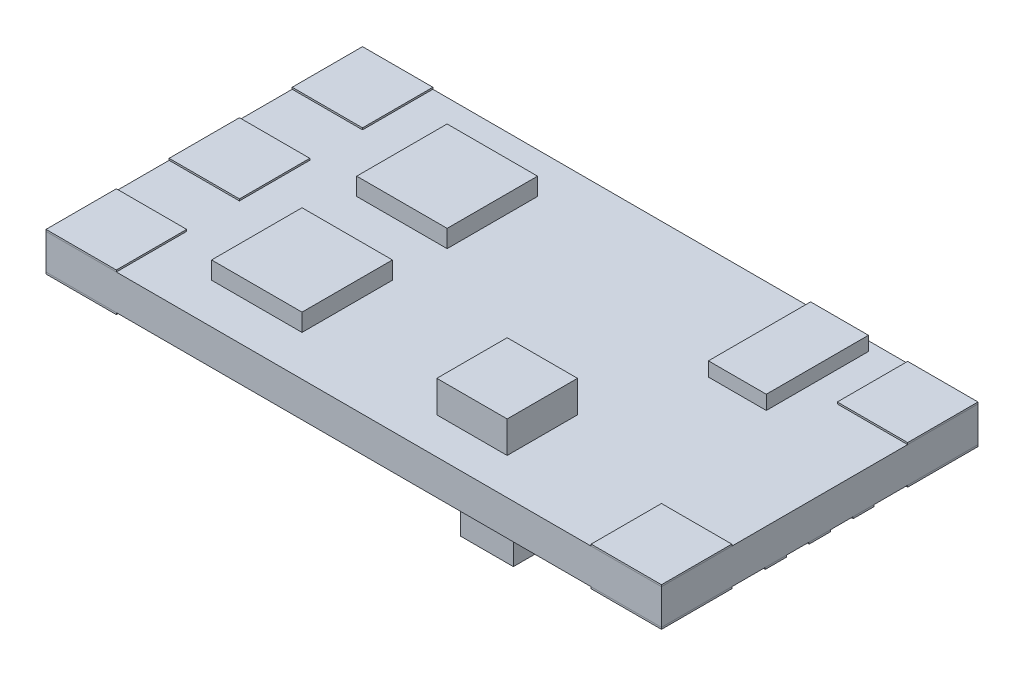
SolidWorks part; units mm, degrees
ref_plane "Front Plane" through (0, 0, 0) normal (0, 0, 1) x (1, 0, 0)
ref_plane "Top Plane" through (0, 0, 0) normal (0, 1, 0) x (1, 0, 0)
ref_plane "Right Plane" through (0, 0, 0) normal (1, 0, 0) x (0, 0, -1)
sketch "Sketch1" plane through (0, 0, 0) normal (0, 1, 0) x (1, 0, 0)
  line L1 (-17.5, -9) -> (17.5, -9)
  line L2 (-17.5, -9) -> (-17.5, 9)
  line L3 (-17.5, 9) -> (17.5, 9)
  line L4 (17.5, -9) -> (17.5, 9)
  line L5 (0, 9) -> (0, -9) construction
  line L6 (-17.5, 0) -> (17.5, 0) construction
  point P0 (0, 0)
  dimension "D1" = 35
  dimension "D2" = 18
extrude "Boss-Extrude1" add sketch "Sketch1" along normal blind 2
sketch "Sketch2" plane through (0, 2, 0) normal (0, 1, 0) x (1, 0, 0)
  line L1 (8.5094, 2.6608) -> (11.8, 2.6608)
  line L2 (8.5094, 2.6608) -> (8.5094, 8.4708)
  line L3 (8.5094, 8.4708) -> (11.8, 8.4708)
  line L4 (11.8, 2.6608) -> (11.8, 8.4708)
  line L5 (10.1547, 8.4708) -> (10.1547, 2.6608) construction
  line L6 (8.5094, 5.5658) -> (11.8, 5.5658) construction
  point P0 (10.1547, 5.5658)
extrude "Boss-Extrude2" add sketch "Sketch2" along normal blind 0.8 separate body
sketch "Sketch3" plane through (0, 2, 0) normal (0, 1, 0) x (1, 0, 0)
  line L1 (2.6479, -6.9231) -> (6.6479, -6.9231)
  line L2 (2.6479, -6.9231) -> (2.6479, -2.9231)
  line L3 (2.6479, -2.9231) -> (6.6479, -2.9231)
  line L4 (6.6479, -6.9231) -> (6.6479, -2.9231)
  line L5 (4.6479, -2.9231) -> (4.6479, -6.9231) construction
  line L6 (2.6479, -4.9231) -> (6.6479, -4.9231) construction
  point P0 (4.6479, -4.9231)
  dimension "D1" = 4
extrude "Boss-Extrude3" add sketch "Sketch3" along normal blind 1.8 separate body
sketch "Sketch4" plane through (0, 2, 0) normal (0, 1, 0) x (1, 0, 0)
  line L0 (-17.5, 0) -> (17.5, 0) construction
  line L5 (-17.5, 9) -> (-17.5, -9) construction
  line L6 (17.5, -9) -> (17.5, 9) construction
  line L7 (-10.3861, -6.697) -> (-5.2444, -6.697)
  line L8 (-10.3861, -6.697) -> (-10.3861, -1.5553)
  line L9 (-10.3861, -1.5553) -> (-5.2444, -1.5553)
  line L10 (-5.2444, -6.697) -> (-5.2444, -1.5553)
  line L11 (-7.8153, -1.5553) -> (-7.8153, -6.697) construction
  line L12 (-10.3861, -4.1261) -> (-5.2444, -4.1261) construction
  line L13 (-10.3861, 1.5553) -> (-5.2444, 1.5553)
  line L14 (-5.2444, 6.697) -> (-5.2444, 1.5553)
  line L15 (-10.3861, 6.697) -> (-5.2444, 6.697)
  line L16 (-10.3861, 6.697) -> (-10.3861, 1.5553)
  point P4 (-7.8153, -4.1261)
extrude "Boss-Extrude4" add sketch "Sketch4" along normal blind 1 separate body
sketch "Sketch5" plane through (0, 2, 0) normal (0, 1, 0) x (1, 0, 0)
  line L0 (-17.5, 9) -> (-17.5, -9) construction
  line L1 (-13.5, 5) -> (-17.5, 5)
  line L2 (-13.5, 5) -> (-13.5, 9)
  line L3 (-13.5, 9) -> (-17.5, 9)
  line L4 (-17.5, 5) -> (-17.5, 9)
  line L5 (-15.5, 9) -> (-15.5, 5) construction
  line L6 (-13.5, 7) -> (-17.5, 7) construction
  line L7 (-13.5, -2) -> (-17.5, -2)
  line L8 (-13.5, -2) -> (-13.5, 2)
  line L9 (-13.5, 2) -> (-17.5, 2)
  line L10 (-17.5, -2) -> (-17.5, 2)
  line L11 (-15.5, 2) -> (-15.5, -2) construction
  line L12 (-13.5, 0) -> (-17.5, 0) construction
  line L13 (13.5, -9) -> (17.5, -9)
  line L14 (-13.5, -5) -> (-17.5, -5)
  line L15 (-13.5, -5) -> (-13.5, -9)
  line L16 (-13.5, -9) -> (-17.5, -9)
  line L17 (-17.5, -5) -> (-17.5, -9)
  line L18 (-15.5, -9) -> (-15.5, -5) construction
  line L19 (-13.5, -7) -> (-17.5, -7) construction
  line L20 (13.5, 5) -> (17.5, 5)
  line L21 (13.5, 5) -> (13.5, 9)
  line L22 (13.5, 9) -> (17.5, 9)
  line L23 (17.5, 5) -> (17.5, 9)
  line L24 (15.5, 9) -> (15.5, 5) construction
  line L25 (13.5, 7) -> (17.5, 7) construction
  line L26 (17.5, -5) -> (17.5, -9)
  line L27 (13.5, -5) -> (17.5, -5)
  line L28 (13.5, -5) -> (13.5, -9)
  point P0 (-15.5, 7)
  point P4 (-15.5, 0)
  point P10 (-15.5, -7)
  point P14 (15.5, 7)
  dimension "D1" = 4
extrude "Boss-Extrude5" add sketch "Sketch5" along normal blind 0.1 separate body
ref_plane "Plane1" through (0, 1, 0) normal (0, 1, 0) x (1, 0, 0)
mirror "Mirror1" about plane through (0, 1, 0) normal (0, 1, 0) of bodies 106 107 108 109 110
sketch "Sketch6" plane through (0, 0, 0) normal (0, -1, 0) x (1, 0, 0)
  line L0 (-4, 9) -> (-4, -9) construction
  line L1 (-17.5, 9) -> (17.5, 9) construction
  line L2 (17.5, -9) -> (-17.5, -9) construction
  line L3 (-17.5, -9) -> (-17.5, 9) construction
  line L4 (-11.5, -8.238) -> (-4.8052, -8.238)
  line L5 (-11.5, 3.762) -> (-4.8052, 3.762)
  line L6 (-11.5, 3.762) -> (-11.5, 8.238)
  line L7 (-11.5, 8.238) -> (-4.8052, 8.238)
  line L8 (-4.8052, 3.762) -> (-4.8052, 8.238)
  line L9 (-8.1526, 8.238) -> (-8.1526, 3.762) construction
  line L10 (-11.5, 6) -> (-4.8052, 6) construction
  line L11 (-11.5, -2.238) -> (-4.8052, -2.238)
  line L12 (-11.5, -2.238) -> (-11.5, 2.238)
  line L13 (-11.5, 2.238) -> (-4.8052, 2.238)
  line L14 (-4.8052, -2.238) -> (-4.8052, 2.238)
  line L15 (-8.1526, 2.238) -> (-8.1526, -2.238) construction
  line L16 (-11.5, 0) -> (-4.8052, 0) construction
  line L17 (-4.8052, -3.762) -> (-4.8052, -8.238)
  line L18 (-11.5, -3.762) -> (-4.8052, -3.762)
  line L19 (-11.5, -3.762) -> (-11.5, -8.238)
  line L20 (3.5, -3.762) -> (3.5, -8.238)
  line L21 (3.5, -3.762) -> (-3.1948, -3.762)
  line L22 (-3.1948, -3.762) -> (-3.1948, -8.238)
  line L23 (3.5, -8.238) -> (-3.1948, -8.238)
  line L24 (3.5, 2.238) -> (-3.1948, 2.238)
  line L25 (-3.1948, -2.238) -> (-3.1948, 2.238)
  line L26 (3.5, -2.238) -> (-3.1948, -2.238)
  line L27 (3.5, -2.238) -> (3.5, 2.238)
  line L28 (3.5, 8.238) -> (-3.1948, 8.238)
  line L29 (-3.1948, 3.762) -> (-3.1948, 8.238)
  line L30 (3.5, 3.762) -> (-3.1948, 3.762)
  line L31 (3.5, 3.762) -> (3.5, 8.238)
  point P8 (-8.1526, 6)
  point P12 (-8.1526, 0)
  dimension "D1" = 13.5
  dimension "D2" = 6
  dimension "D3" = 6
extrude "Boss-Extrude6" add sketch "Sketch6" along normal blind 0.7 separate body
sketch "Sketch7" plane through (0, 0, 0) normal (0, -1, 0) x (1, 0, 0)
  line L0 (7, 9) -> (7, -9) construction
  line L1 (-17.5, 9) -> (17.5, 9) construction
  line L2 (17.5, -9) -> (-17.5, -9) construction
  line L3 (17.5, 9) -> (17.5, -9) construction
  line L4 (5.5, 4.6444) -> (5.5, 6.2444)
  line L5 (5.5, 6.8222) -> (8.5, 6.8222)
  line L6 (5.5, 6.8222) -> (5.5, 8.4222)
  line L7 (5.5, 8.4222) -> (8.5, 8.4222)
  line L8 (8.5, 6.8222) -> (8.5, 8.4222)
  line L9 (7, 8.4222) -> (7, 6.8222) construction
  line L10 (5.5, 7.6222) -> (8.5, 7.6222) construction
  line L11 (5.5, 4.6444) -> (8.5, 4.6444)
  line L12 (8.5, 4.6444) -> (8.5, 6.2444)
  line L13 (5.5, 6.2444) -> (8.5, 6.2444)
  line L14 (5.5, 2.4667) -> (5.5, 4.0667)
  line L15 (5.5, 2.4667) -> (8.5, 2.4667)
  line L16 (8.5, 2.4667) -> (8.5, 4.0667)
  line L17 (5.5, 4.0667) -> (8.5, 4.0667)
  line L18 (5.5, 0.2889) -> (5.5, 1.8889)
  line L19 (5.5, 0.2889) -> (8.5, 0.2889)
  line L20 (8.5, 0.2889) -> (8.5, 1.8889)
  line L21 (5.5, 1.8889) -> (8.5, 1.8889)
  line L22 (5.5, -1.8889) -> (5.5, -0.2889)
  line L23 (5.5, -1.8889) -> (8.5, -1.8889)
  line L24 (8.5, -1.8889) -> (8.5, -0.2889)
  line L25 (5.5, -0.2889) -> (8.5, -0.2889)
  line L26 (5.5, -4.0667) -> (5.5, -2.4667)
  line L27 (5.5, -4.0667) -> (8.5, -4.0667)
  line L28 (8.5, -4.0667) -> (8.5, -2.4667)
  line L29 (5.5, -2.4667) -> (8.5, -2.4667)
  line L30 (5.5, -6.2444) -> (5.5, -4.6444)
  line L31 (5.5, -6.2444) -> (8.5, -6.2444)
  line L32 (8.5, -6.2444) -> (8.5, -4.6444)
  line L33 (5.5, -4.6444) -> (8.5, -4.6444)
  line L34 (5.5, -8.4222) -> (5.5, -6.8222)
  line L35 (5.5, -8.4222) -> (8.5, -8.4222)
  line L36 (8.5, -8.4222) -> (8.5, -6.8222)
  line L37 (5.5, -6.8222) -> (8.5, -6.8222)
  line L38 (8.5, -8.4222) -> (8.5, -9) construction
  line L39 (8.5, 8.4222) -> (8.5, 9) construction
  line L40 (8.5, 6.8222) -> (8.5, 6.2444) construction
  point P8 (7, 7.6222)
  dimension "D1" = 10.5
  dimension "D3" = 1.6
  dimension "D4" = 3
  dimension "D2" = 8
extrude "Boss-Extrude7" add sketch "Sketch7" along normal blind 1.8 separate body
sketch "Sketch8" plane through (0, 0, 0) normal (0, -1, 0) x (1, 0, 0)
  line L0 (17.5, 9) -> (17.5, -9) construction
  line L1 (15.5, -0.6) -> (17.5, -0.6)
  line L2 (15.5, -0.6) -> (15.5, 0.6)
  line L3 (15.5, 0.6) -> (17.5, 0.6)
  line L4 (17.5, -0.6) -> (17.5, 0.6)
  line L5 (16.5, 0.6) -> (16.5, -0.6) construction
  line L6 (15.5, 0) -> (17.5, 0) construction
  line L7 (15.5, 1.9) -> (17.5, 1.9)
  line L8 (15.5, 1.9) -> (15.5, 3.1)
  line L9 (15.5, 3.1) -> (17.5, 3.1)
  line L10 (17.5, 1.9) -> (17.5, 3.1)
  line L11 (16.5, 3.1) -> (16.5, 1.9) construction
  line L12 (15.5, 2.5) -> (17.5, 2.5) construction
  line L13 (15.5, -3.1) -> (17.5, -3.1)
  line L14 (17.5, -1.9) -> (17.5, -3.1)
  line L15 (15.5, -1.9) -> (17.5, -1.9)
  line L16 (15.5, -1.9) -> (15.5, -3.1)
  point P0 (16.5, 0)
  point P4 (16.5, 2.5)
  point P8 (0, 0)
  point P9 (0, 0)
  dimension "D1" = 2.5
  dimension "D2" = 2
  dimension "D3" = 1.2
extrude "Boss-Extrude8" add sketch "Sketch8" along normal up to surface (0.1 mm away) separate body up to face at (15.5, -0.1, 7)
sketch "Sketch9" plane through (0, 0, 0) normal (0, -1, 0) x (1, 0, 0)
  line L0 (17.5, 9) -> (17.5, -9) construction
  line L1 (11.5, -1) -> (13.5, -1)
  line L2 (11.5, -1) -> (11.5, 1)
  line L3 (11.5, 1) -> (13.5, 1)
  line L4 (13.5, -1) -> (13.5, 1)
  line L5 (12.5, 1) -> (12.5, -1) construction
  line L6 (11.5, 0) -> (13.5, 0) construction
  point P0 (12.5, 0)
  dimension "D1" = 5
  dimension "D2" = 2
extrude "Boss-Extrude9" add sketch "Sketch9" along normal blind 1 separate body
